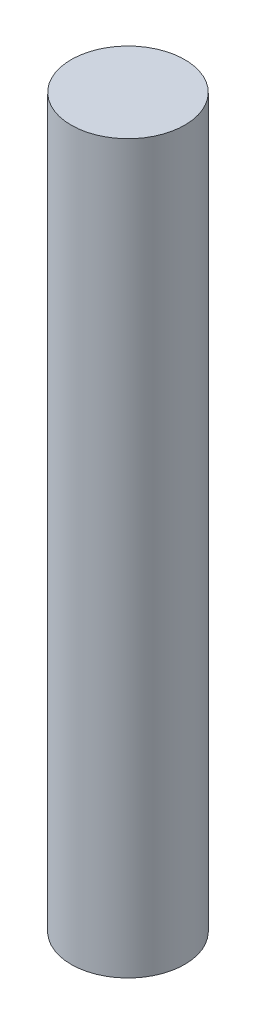
SolidWorks part; units mm, degrees
ref_plane "Front Plane" through (0, 0, 0) normal (0, 0, 1) x (1, 0, 0)
ref_plane "Top Plane" through (0, 0, 0) normal (0, 1, 0) x (1, 0, 0)
ref_plane "Right Plane" through (0, 0, 0) normal (1, 0, 0) x (0, 0, -1)
sketch "Sketch1" plane through (0, 0, 0) normal (0, 1, 0) x (1, 0, 0)
  circle A0 centre (0, 0) radius 0.9922
  dimension "D1" = 1.9844
extrude "Boss-Extrude1" add sketch "Sketch1" along normal blind 12.7
